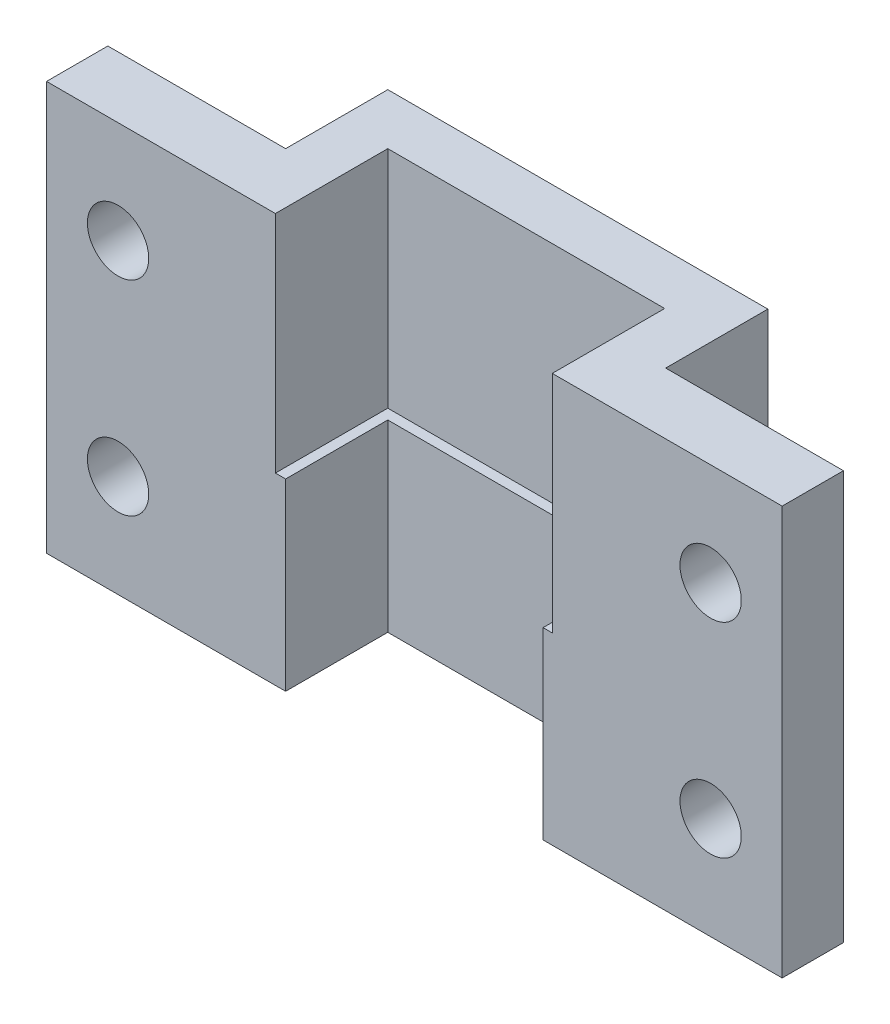
SolidWorks part; units mm, degrees
ref_plane "Front Plane" through (0, 0, 0) normal (0, 0, 1) x (1, 0, 0)
ref_plane "Top Plane" through (0, 0, 0) normal (0, 1, 0) x (1, 0, 0)
ref_plane "Right Plane" through (0, 0, 0) normal (1, 0, 0) x (0, 0, -1)
sketch "Sketch1" plane through (0, 0, 0) normal (0, 1, 0) x (1, 0, 0)
  line L0 (16.7704, -3) -> (28.4704, -3)
  line L1 (1.1704, 5) -> (19.7704, 5)
  line L2 (-7.5296, 0) -> (-7.5296, -3)
  line L3 (-7.5296, -3) -> (4.1704, -3)
  line L4 (28.4704, 0) -> (28.4704, -3)
  line L6 (4.1704, -3) -> (4.1704, 2)
  line L7 (4.1704, 2) -> (16.7704, 2)
  line L8 (16.7704, -3) -> (16.7704, 2)
  line L17 (1.1704, 5) -> (1.1704, 0)
  line L18 (1.1704, 0) -> (-7.5296, 0)
  line L19 (19.7704, 5) -> (19.7704, 0)
  line L20 (19.7704, 0) -> (28.4704, 0)
  dimension "D1" = 36
  dimension "D2" = 3
  dimension "D3" = 11.7
  dimension "D4" = 11.7
  dimension "D5" = 5
  dimension "D6" = 3
  dimension "D7" = 3
  dimension "D8" = 3
  dimension "D9" = 8.7
extrude "Boss-Extrude1" add sketch "Sketch1" along normal blind 20
sketch "Sketch2" plane through (0, 0, 0) normal (0, 0, -1) x (-1, 0, 0)
  line L0 (-1.1704, 20) -> (7.5296, 20) construction
  line L1 (7.5296, 20) -> (7.5296, 0) construction
  line L2 (-28.4704, 20) -> (-28.4704, 0) construction
  line L3 (-28.4704, 20) -> (-19.7704, 20) construction
  circle A0 centre (4.0296, 15) radius 1.5
  circle A1 centre (4.0296, 5) radius 1.5
  circle A2 centre (-24.9704, 5) radius 1.5
  circle A3 centre (-24.9704, 15) radius 1.5
  dimension "D5" = 3
  dimension "D6" = 3
  dimension "D1" = 5
  dimension "D2" = 3.5
  dimension "D3" = 3.5
  dimension "D4" = 10
  dimension "D7" = 3.5
  dimension "D8" = 3.5
  dimension "D9" = 5
  dimension "D10" = 10
extrude "Cut-Extrude1" cut sketch "Sketch2" against normal blind 16
sketch "Sketch3" plane through (0, 20, 0) normal (0, 1, 0) x (1, 0, 0)
  line L0 (4.1704, -3) -> (4.1704, 2) construction
  line L1 (4.1704, 2) -> (16.7704, 2) construction
  line L2 (16.7704, 2) -> (16.7704, -3) construction
  line L3 (4.1704, -3) -> (4.1704, 2)
  line L4 (4.1704, 2) -> (16.7704, 2)
  line L5 (16.7704, 2) -> (16.7704, -3)
  line L6 (3.6704, -3) -> (3.6704, 2.5)
  line L7 (3.6704, 2.5) -> (17.2204, 2.5)
  line L9 (17.2204, -3) -> (16.7704, -3)
  line L10 (4.1704, -3) -> (3.6704, -3)
  line L11 (17.2204, -3) -> (17.2204, 2.5)
  line L13 (3.6704, 2.5) -> (17.2704, 2.5) construction
  line L14 (17.2704, 2.5) -> (17.2704, -3) construction
  dimension "D1" = 0.5
extrude "Cut-Extrude2" cut sketch "Sketch3" against normal blind 11
